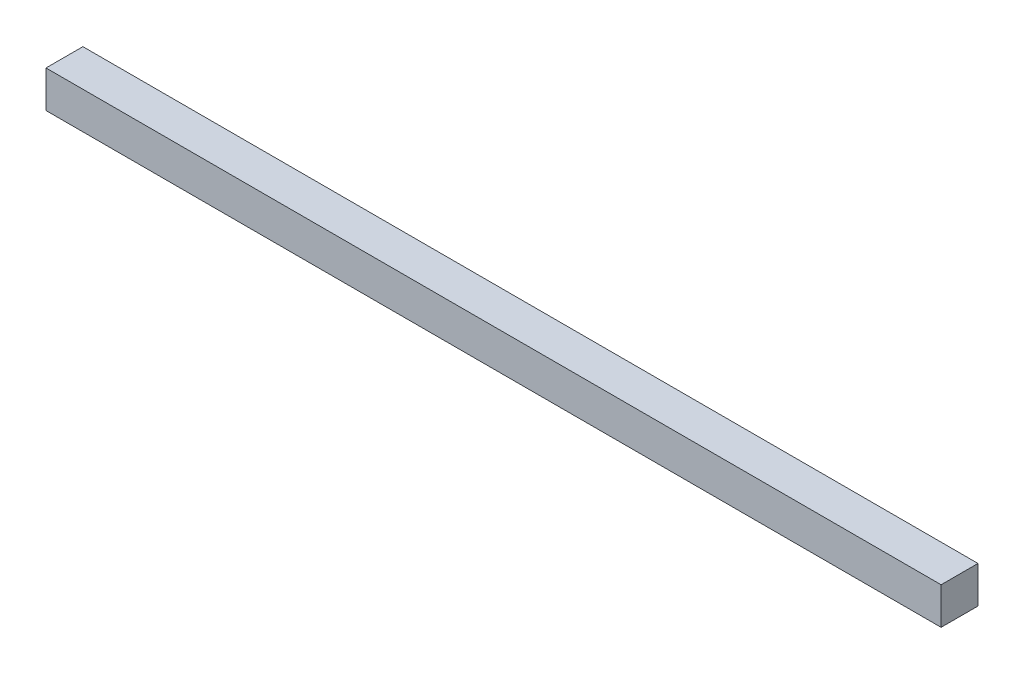
SolidWorks part; units mm, degrees
ref_plane "Front Plane" through (0, 0, 0) normal (0, 0, 1) x (1, 0, 0)
ref_plane "Top Plane" through (0, 0, 0) normal (0, 1, 0) x (1, 0, 0)
ref_plane "Right Plane" through (0, 0, 0) normal (1, 0, 0) x (0, 0, -1)
sketch "Sketch1" plane through (0, 0, 0) normal (0, 1, 0) x (1, 0, 0)
  line L1 (-231.07, 9.525) -> (231.07, 9.525)
  line L2 (-231.07, 9.525) -> (-231.07, -9.525)
  line L3 (-231.07, -9.525) -> (231.07, -9.525)
  line L4 (231.07, 9.525) -> (231.07, -9.525)
  line L5 (-231.07, 9.525) -> (231.07, -9.525) construction
  line L6 (-231.07, -9.525) -> (231.07, 9.525) construction
  point P0 (0, 0)
  dimension "D1" = 462.14
  dimension "D2" = 19.05
extrude "Boss-Extrude1" add sketch "Sketch1" along normal blind 19.05
